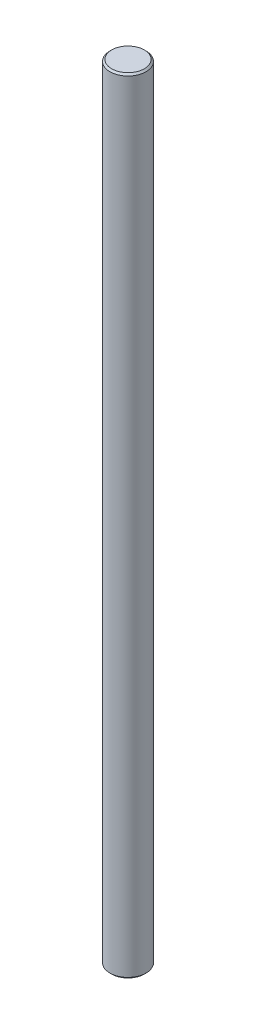
SolidWorks part; units mm, degrees
material "AISI 1035 Acier (SS)"
ref_plane "Plan de face" through (0, 0, 0) normal (0, 0, 1) x (1, 0, 0)
ref_plane "Plan de dessus" through (0, 0, 0) normal (0, 1, 0) x (1, 0, 0)
ref_plane "Plan de droite" through (0, 0, 0) normal (1, 0, 0) x (0, 0, -1)
sketch "Esquisse1" plane through (0, 0, 0) normal (0, 1, 0) x (1, 0, 0)
  circle A0 centre (0, 0) radius 3.175
  dimension "D1" = 6.35
extrude "Boss.-Extru.1" add sketch "Esquisse1" along normal blind 138
chamfer "Chanfrein1" distance 0.3 angle 45 2 edges at (0, 0, 3.175) (0, 138, 3.175)
